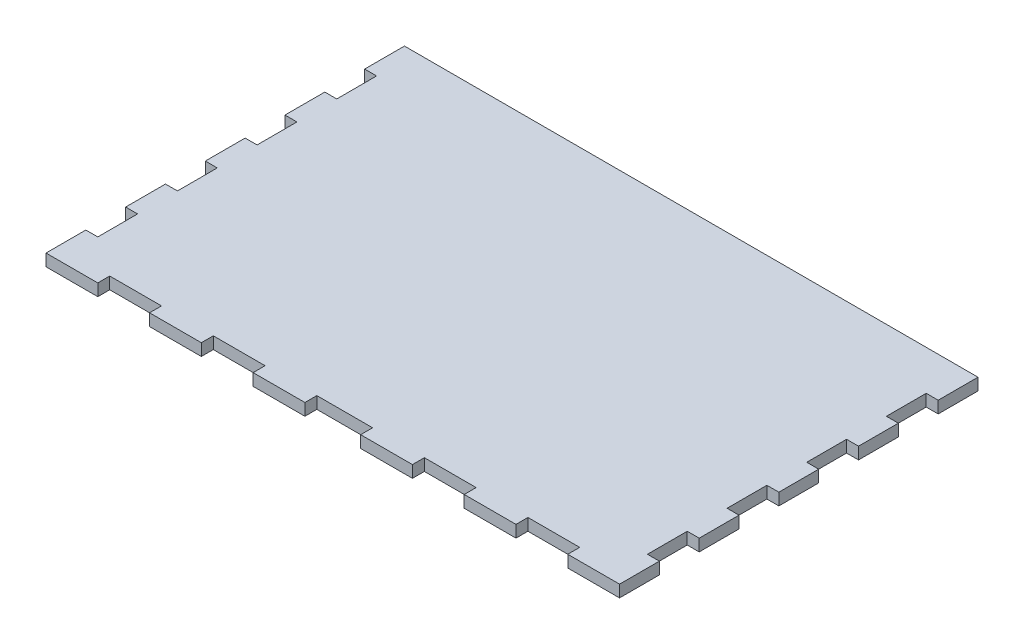
SolidWorks part; units mm, degrees
ref_plane "Front Plane" through (0, 0, 0) normal (0, 0, 1) x (1, 0, 0)
ref_plane "Top Plane" through (0, 0, 0) normal (0, 1, 0) x (1, 0, 0)
ref_plane "Right Plane" through (0, 0, 0) normal (1, 0, 0) x (0, 0, -1)
sketch "Sketch1" plane through (0, 0, 0) normal (0, 1, 0) x (1, 0, 0)
  line L0 (26, 90) -> (39, 90)
  line L1 (0, 0) -> (13, 0)
  line L2 (0, 0) -> (0, 10)
  line L3 (0, 90) -> (13, 90)
  line L4 (144, 0) -> (144, 10)
  line L5 (0, 80) -> (0, 90)
  line L6 (13, 0) -> (13, 3)
  line L7 (13, 3) -> (26, 3)
  line L8 (26, 0) -> (26, 3)
  line L9 (144, 80) -> (141, 80)
  line L10 (39, 0) -> (39, 3)
  line L11 (39, 3) -> (52, 3)
  line L12 (52, 0) -> (52, 3)
  line L13 (13, 90) -> (105, 90)
  line L14 (65, 0) -> (65, 3)
  line L15 (65, 3) -> (79, 3)
  line L16 (79, 0) -> (79, 3)
  line L17 (144, 70) -> (141, 70)
  line L18 (92, 0) -> (92, 3)
  line L19 (92, 3) -> (105, 3)
  line L20 (105, 0) -> (105, 3)
  line L21 (141, 80) -> (141, 70)
  line L22 (118, 0) -> (118, 3)
  line L23 (118, 3) -> (131, 3)
  line L24 (131, 0) -> (131, 3)
  line L25 (52, 0) -> (65, 0)
  line L29 (79, 0) -> (92, 0)
  line L33 (105, 0) -> (118, 0)
  line L37 (131, 0) -> (144, 0)
  line L38 (118, 90) -> (131, 90)
  line L41 (144, 60) -> (141, 60)
  line L45 (52, 90) -> (65, 90)
  line L46 (79, 90) -> (92, 90)
  line L47 (105, 90) -> (118, 90)
  line L48 (131, 90) -> (144, 90)
  line L49 (26, 0) -> (39, 0)
  line L50 (131, 90) -> (130.9762, 89.9539)
  line L51 (144, 50) -> (141, 50)
  line L52 (141, 60) -> (141, 50)
  line L53 (144, 40) -> (141, 40)
  line L55 (144, 30) -> (141, 30)
  line L56 (141, 40) -> (141, 30)
  line L57 (144, 20) -> (141, 20)
  line L59 (144, 10) -> (141, 10)
  line L60 (141, 20) -> (141, 10)
  line L61 (0, 80) -> (3, 80)
  line L62 (144, 60) -> (144, 70)
  line L63 (0, 70) -> (3, 70)
  line L64 (3, 80) -> (3, 70)
  line L65 (0, 60) -> (3, 60)
  line L66 (144, 40) -> (144, 50)
  line L67 (0, 50) -> (3, 50)
  line L68 (3, 60) -> (3, 50)
  line L69 (0, 40) -> (3, 40)
  line L70 (144, 20) -> (144, 30)
  line L71 (0, 30) -> (3, 30)
  line L72 (3, 40) -> (3, 30)
  line L73 (0, 20) -> (3, 20)
  line L75 (0, 10) -> (3, 10)
  line L76 (3, 20) -> (3, 10)
  line L77 (0, 60) -> (0, 70)
  line L78 (0, 40) -> (0, 50)
  line L79 (0, 20) -> (0, 30)
  line L80 (144, 80) -> (144, 90)
  dimension "D1" = 144
  dimension "D2" = 90
  dimension "D3" = 13
  dimension "D4" = 13
  dimension "D5" = 13
  dimension "D6" = 13
  dimension "D7" = 13
  dimension "D8" = 14
  dimension "D9" = 13
  dimension "D10" = 13
  dimension "D11" = 13
  dimension "D12" = 13
  dimension "D13" = 3
  dimension "D25" = 10
  dimension "D26" = 10
  dimension "D27" = 10
  dimension "D28" = 10
  dimension "D29" = 10
  dimension "D30" = 10
  dimension "D31" = 10
  dimension "D32" = 10
  dimension "D33" = 3
  dimension "D34" = 10
  dimension "D35" = 10
  dimension "D36" = 10
  dimension "D37" = 10
  dimension "D38" = 10
  dimension "D39" = 10
  dimension "D40" = 10
  dimension "D41" = 10
  dimension "D42" = 3
extrude "Boss-Extrude2" add sketch "Sketch1" along normal blind 3
